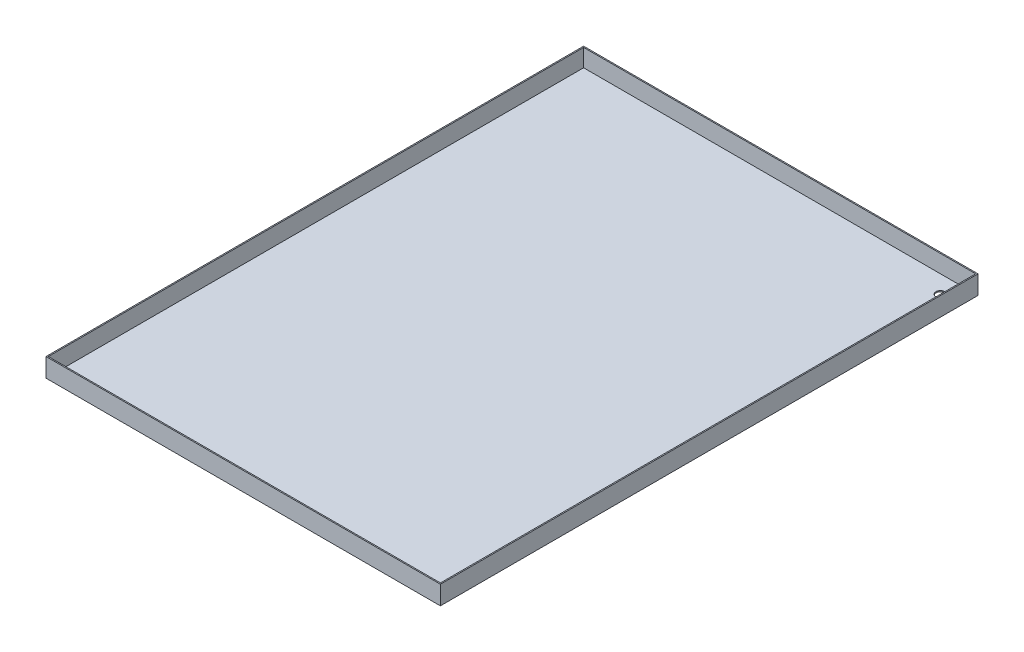
SolidWorks part; units mm, degrees
ref_plane "Front Plane" through (0, 0, 0) normal (0, 0, 1) x (1, 0, 0)
ref_plane "Top Plane" through (0, 0, 0) normal (0, 1, 0) x (1, 0, 0)
ref_plane "Right Plane" through (0, 0, 0) normal (1, 0, 0) x (0, 0, -1)
sketch "Sketch1" plane through (0, 0, 0) normal (0, 1, 0) x (1, 0, 0)
  line L1 (0, 0) -> (559, 0)
  line L2 (0, 0) -> (0, 762)
  line L3 (0, 762) -> (559, 762)
  line L4 (559, 0) -> (559, 762)
  dimension "D1" = 559
  dimension "D2" = 762
extrude "Boss-Extrude1" add sketch "Sketch1" along normal blind 1.6
sketch "Sketch2" plane through (0, 1.6, 0) normal (0, 1, 0) x (1, 0, 0)
  line L5 (559, 0) -> (0, 0)
  line L6 (559, 0) -> (559, 762)
  line L7 (559, 762) -> (0, 762)
  line L8 (1.6, 760.4) -> (1.6, 1.6)
  line L9 (1.6, 1.6) -> (557.4, 1.6)
  line L10 (557.4, 1.6) -> (557.4, 760.4)
  line L11 (557.4, 760.4) -> (1.6, 760.4)
  line L12 (1.6, 760.4) -> (1.6, 1.6)
  line L13 (1.6, 1.6) -> (557.4, 1.6)
  line L14 (557.4, 1.6) -> (557.4, 760.4)
  line L15 (557.4, 760.4) -> (1.6, 760.4)
  line L16 (0, 0) -> (0, 762)
  dimension "D1" = 1.6
extrude "Boss-Extrude2" add sketch "Sketch2" along normal blind 25
sketch "Sketch3" plane through (0, 1.6, 0) normal (0, 1, 0) x (1, 0, 0)
  line L1 (557.4, 760.4) -> (532.4, 760.4)
  line L2 (557.4, 760.4) -> (557.4, 735.4)
  line L3 (557.4, 735.4) -> (532.4, 735.4)
  line L4 (532.4, 760.4) -> (532.4, 735.4)
  circle A0 centre (532.4, 735.4) radius 6.35
  dimension "D1" = 25
  dimension "D2" = 25
extrude "Cut-Extrude1" cut sketch "Sketch3" against normal through all contours A0
